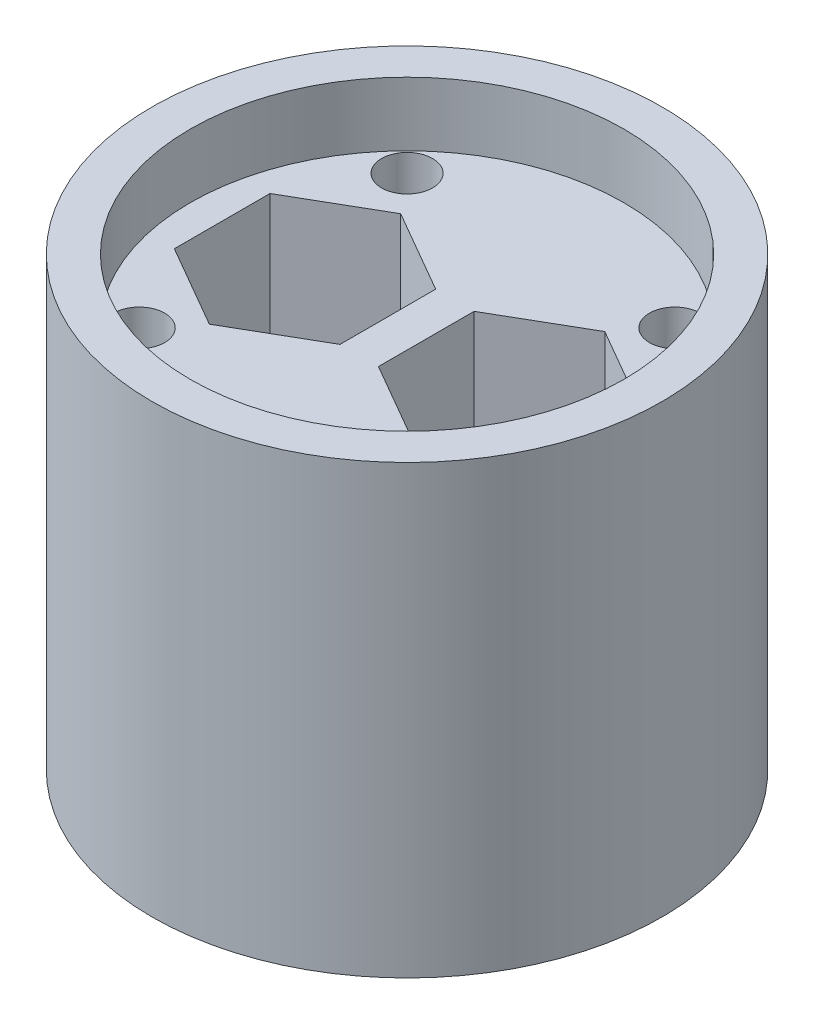
SolidWorks part; units mm, degrees
ref_plane "Спереди" through (0, 0, 0) normal (0, 0, 1) x (1, 0, 0)
ref_plane "Сверху" through (0, 0, 0) normal (0, 1, 0) x (1, 0, 0)
ref_plane "Справа" through (0, 0, 0) normal (1, 0, 0) x (0, 0, -1)
sketch "Sketch1" plane through (0, 0, 0) normal (0, 1, 0) x (1, 0, 0)
  line L1 (14.1421, -14.1421) -> (-14.1421, -14.1421) construction
  line L2 (14.1421, -14.1421) -> (14.1421, 14.1421) construction
  line L3 (14.1421, 14.1421) -> (-14.1421, 14.1421) construction
  line L4 (-14.1421, -14.1421) -> (-14.1421, 14.1421) construction
  line L5 (14.1421, -14.1421) -> (-14.1421, 14.1421) construction
  line L6 (14.1421, 14.1421) -> (-14.1421, -14.1421) construction
  circle A0 centre (0, 0) radius 20
  point P0 (0, 0)
  dimension "D1" = 40
extrude "Boss-Extrude1" add sketch "Sketch1" along normal blind 35
sketch "Sketch2" plane through (0, 35, 0) normal (0, 1, 0) x (1, 0, 0)
  line L0 (-20, 0) -> (20, 0) construction
  line L1 (-8, 7.5) -> (-14.4952, 3.75)
  line L2 (-14.4952, 3.75) -> (-14.4952, -3.75)
  line L3 (-14.4952, -3.75) -> (-8, -7.5)
  line L4 (-8, -7.5) -> (-1.5048, -3.75)
  line L5 (-1.5048, -3.75) -> (-1.5048, 3.75)
  line L6 (-1.5048, 3.75) -> (-8, 7.5)
  line L8 (8, 7.5) -> (1.5048, 3.75)
  line L9 (1.5048, 3.75) -> (1.5048, -3.75)
  line L10 (1.5048, -3.75) -> (8, -7.5)
  line L11 (8, -7.5) -> (14.4952, -3.75)
  line L12 (14.4952, -3.75) -> (14.4952, 3.75)
  line L13 (14.4952, 3.75) -> (8, 7.5)
  circle A0 centre (-8, 0) radius 7.5 construction
  circle A1 centre (0, 0) radius 20 construction
  circle A2 centre (8, 0) radius 7.5 construction
  point P25 (0, 0)
  dimension "D1" = 15
  dimension "D2" = 16
  dimension "D3" = 8
extrude "Cut-Extrude1" cut sketch "Sketch2" against normal blind 15
sketch "Sketch3" plane through (0, 20, 0) normal (0, 1, 0) x (1, 0, 0)
  line L0 (-8, 7.5) -> (-8, -7.5) construction
  line L1 (8, 7.5) -> (8, -7.5) construction
  circle A0 centre (-8, 0) radius 4.1
  circle A1 centre (8, 0) radius 4.1
  point P12 (-8, 0)
  dimension "D1" = 8.2
extrude "Cut-Extrude2" cut sketch "Sketch3" against normal through all
sketch "Sketch4" plane through (0, 35, 0) normal (0, 1, 0) x (1, 0, 0)
  line L1 (10.5, -10.5) -> (-10.5, -10.5) construction
  line L2 (10.5, -10.5) -> (10.5, 10.5) construction
  line L3 (10.5, 10.5) -> (-10.5, 10.5) construction
  line L4 (-10.5, -10.5) -> (-10.5, 10.5) construction
  line L5 (10.5, -10.5) -> (-10.5, 10.5) construction
  line L6 (10.5, 10.5) -> (-10.5, -10.5) construction
  circle A0 centre (-10.5, 10.5) radius 2
  circle A1 centre (10.5, 10.5) radius 2
  circle A2 centre (10.5, -10.5) radius 2
  circle A3 centre (-10.5, -10.5) radius 2
  point P0 (0, 0)
  dimension "D1" = 4
  dimension "D2" = 21
extrude "Cut-Extrude3" cut sketch "Sketch4" against normal through all
sketch "Sketch5" plane through (0, 35, 0) normal (0, 1, 0) x (1, 0, 0)
  circle A0 centre (0, 0) radius 17
  circle A1 centre (0, 0) radius 20 construction
  dimension "D1" = 3
extrude "Cut-Extrude4" cut sketch "Sketch5" against normal blind 5
sketch "Sketch6" plane through (0, 0, 0) normal (0, -1, 0) x (1, 0, 0)
  line L0 (8, -8.1) -> (-8, -8.1)
  line L1 (8, 8.1) -> (-8, 8.1)
  circle A0 centre (8, 0) radius 8.1 construction
  circle A1 centre (-8, 0) radius 8.1 construction
  arc A2 (8, -8.1) -> (8, 8.1) centre (8, 0) ccw
  arc A3 (-8, -8.1) -> (-8, 8.1) centre (-8, 0) cw
  dimension "D1" = 16.2
extrude "Cut-Extrude5" cut sketch "Sketch6" against normal blind 2
